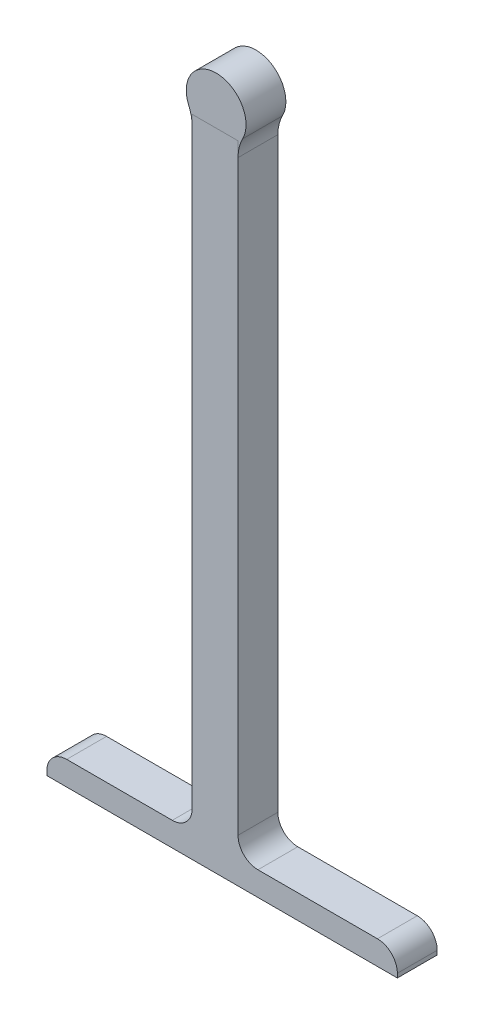
SolidWorks part; units mm, degrees
ref_plane "Front Plane" through (0, 0, 0) normal (0, 0, 1) x (1, 0, 0)
ref_plane "Top Plane" through (0, 0, 0) normal (0, 1, 0) x (1, 0, 0)
ref_plane "Right Plane" through (0, 0, 0) normal (1, 0, 0) x (0, 0, -1)
sketch "Sketch1" plane through (0, 0, 0) normal (0, 0, 1) x (1, 0, 0)
  circle A0 centre (0, 0) radius 7.5
  dimension "D1" = 15
extrude "Boss-Extrude2" add sketch "Sketch1" along normal blind 10
sketch "Sketch3" plane through (0, 0, 10) normal (0, 0, 1) x (1, 0, 0)
  line L1 (-6.0118, -4.4842) -> (5.4882, -4.4842)
  line L2 (-6.0118, -4.4842) -> (-6.0118, -166.4842)
  line L3 (-6.0118, -166.4842) -> (5.4882, -166.4842)
  line L4 (5.4882, -4.4842) -> (5.4882, -166.4842)
  circle A0 centre (0, 0) radius 7.5 construction
  dimension "D1" = 11.5
  dimension "D2" = 162
extrude "Boss-Extrude3" add sketch "Sketch3" along normal blind 0.001 and the other way blind 10
sketch "Sketch4" plane through (5.4882, 0, 0) normal (1, 0, 0) x (0, 0, -1)
  line L0 (0, -166.4842) -> (0, -5.1117) construction
  line L1 (-10.001, -166.4842) -> (0, -166.4842)
  line L2 (-10.001, -166.4842) -> (-10.001, -160.4545)
  line L3 (-10.001, -160.4545) -> (0, -160.4545)
  line L4 (0, -166.4842) -> (0, -160.4545)
extrude "Boss-Extrude4" add sketch "Sketch4" along normal blind 40 and the other way blind 48
fillet "Fillet1" radius 10 1 edges at (5.4882, -5.1117, 5)
fillet "Fillet2" radius 10 1 edges at (-6.0118, -4.4842, 5)
fillet "Fillet3" radius 5 1 edges at (5.4882, -160.4545, 5.0005)
fillet "Fillet4" radius 5 1 edges at (-6.0118, -160.4545, 5.0005)
fillet "Fillet5" radius 5 1 edges at (-42.5118, -160.4545, 5.0005)
fillet "Fillet6" radius 5 1 edges at (45.4882, -160.4545, 5.0005)
